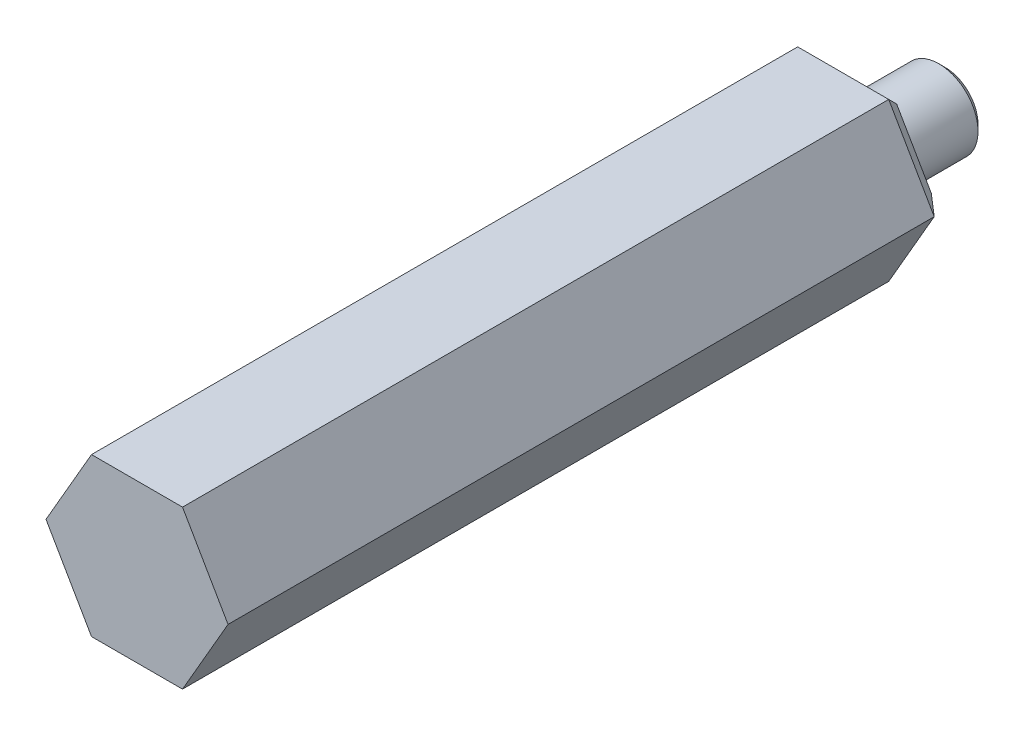
SolidWorks part; units mm, degrees
material "Alloy Steel"
ref_plane "Front Plane" through (0, 0, 0) normal (0, 0, 1) x (1, 0, 0)
ref_plane "Top Plane" through (0, 0, 0) normal (0, 1, 0) x (1, 0, 0)
ref_plane "Right Plane" through (0, 0, 0) normal (1, 0, 0) x (0, 0, -1)
sketch "Sketch1" plane through (0, 0, 0) normal (0, 1, 0) x (1, 0, 0)
  line L0 (7.366, -29.337) -> (7.366, 29.337)
  line L1 (7.366, 29.337) -> (3.1623, 29.337)
  line L2 (3.1623, 29.337) -> (3.1623, 36.068)
  line L3 (0, 36.068) -> (0, -29.337)
  line L4 (3.1623, 36.068) -> (0, 36.068)
  line L5 (0, 0) -> (7.366, 0) construction
  line L6 (7.366, -29.337) -> (0, -29.337)
  line L16 (0, -29.337) -> (0, 36.068) construction
  dimension "D1" = 65.405
  dimension "D2" = 14.732
  dimension "D3" = 6.731
  dimension "D4" = 6.3246
  dimension "D5" = 58.674
revolve "Revolve1" add sketch "Sketch1" angle 360 about L3
chamfer "Chamfer1" distance 0.508 angle 45 1 edges at (-3.1623, 0, -36.068)
sketch "Sketch2" plane through (0, 0, -29.337) normal (0, 0, -1) x (-1, 0, 0)
  line L0 (-7.366, 0) -> (7.366, 0) construction
  line L1 (-7.366, 0) -> (-3.683, -6.3791)
  line L2 (-3.683, -6.3791) -> (3.683, -6.3791)
  line L3 (3.683, -6.3791) -> (7.366, 0)
  line L4 (7.366, 0) -> (3.683, 6.3791)
  line L5 (3.683, 6.3791) -> (-3.683, 6.3791)
  line L6 (-3.683, 6.3791) -> (-7.366, 0)
  circle A0 centre (0, 0) radius 6.3791 construction
  circle A1 centre (0, 0) radius 7.366 construction
  circle A2 centre (0, 0) radius 7.366
  circle M2 centre (0, 0) radius 7.366
extrude "Extrude1" cut sketch "Sketch2" against normal up to next contours L5 M2 | L4 M2 | L3 M2 | L2 M2 | L1 M2 | L6 M2
chamfer "Chamfer2" distance 1.524 angle 45 6 edges at (5.5245, 3.1896, -29.337) (5.5245, -3.1896, -29.337) (0, -6.3791, -29.337) (-5.5245, -3.1896, -29.337) (-5.5245, 3.1896, -29.337) (0, 6.3791, -29.337)
